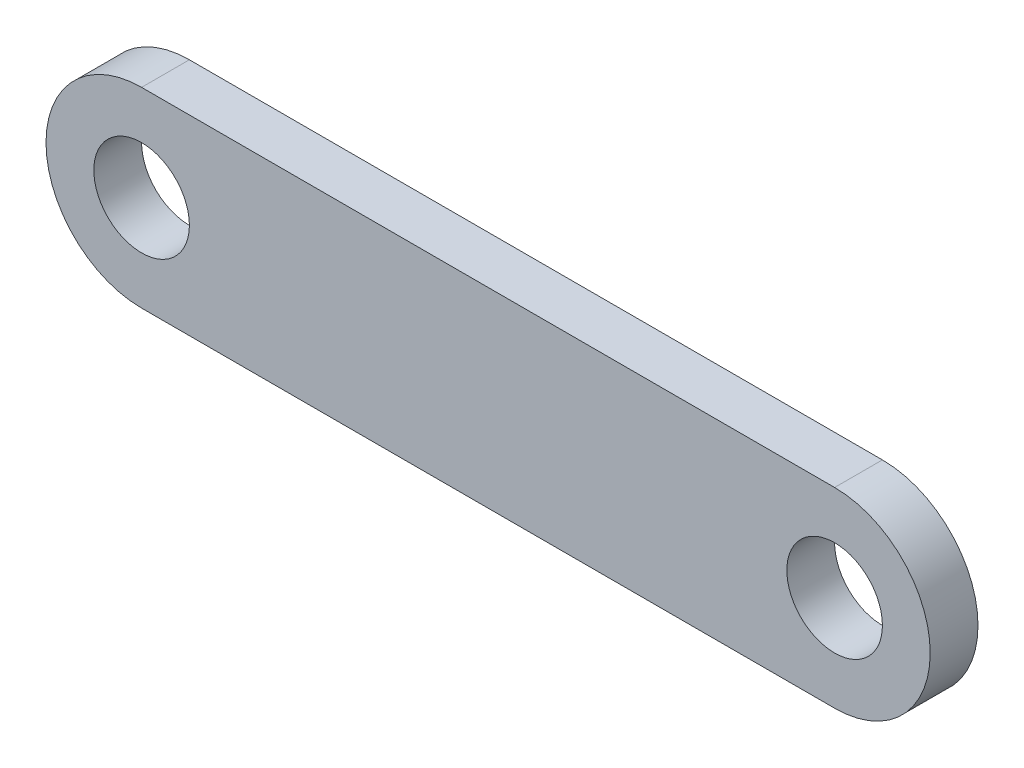
SolidWorks part; units mm, degrees
ref_plane "Front Plane" through (0, 0, 0) normal (0, 0, 1) x (1, 0, 0)
ref_plane "Top Plane" through (0, 0, 0) normal (0, 1, 0) x (1, 0, 0)
ref_plane "Right Plane" through (0, 0, 0) normal (1, 0, 0) x (0, 0, -1)
sketch "Sketch1" plane through (0, 0, 0) normal (0, 0, 1) x (1, 0, 0)
  line L0 (0, 0) -> (-36.83, 0) construction
  line L1 (0, -5.08) -> (-36.83, -5.08)
  line L2 (0, 5.08) -> (-36.83, 5.08)
  arc A0 (0, -5.08) -> (0, 5.08) centre (0, 0) ccw
  arc A1 (-36.83, 5.08) -> (-36.83, -5.08) centre (-36.83, 0) ccw
  circle A2 centre (-36.83, 0) radius 2.54
  circle A3 centre (0, 0) radius 2.54
  point P3 (-18.415, 0)
  dimension "D2" = 5.08
  dimension "D3" = 5.08
  dimension "D4" = 5.08
  dimension "D1" = 36.83
extrude "Boss-Extrude1" add sketch "Sketch1" along normal blind 2.54
